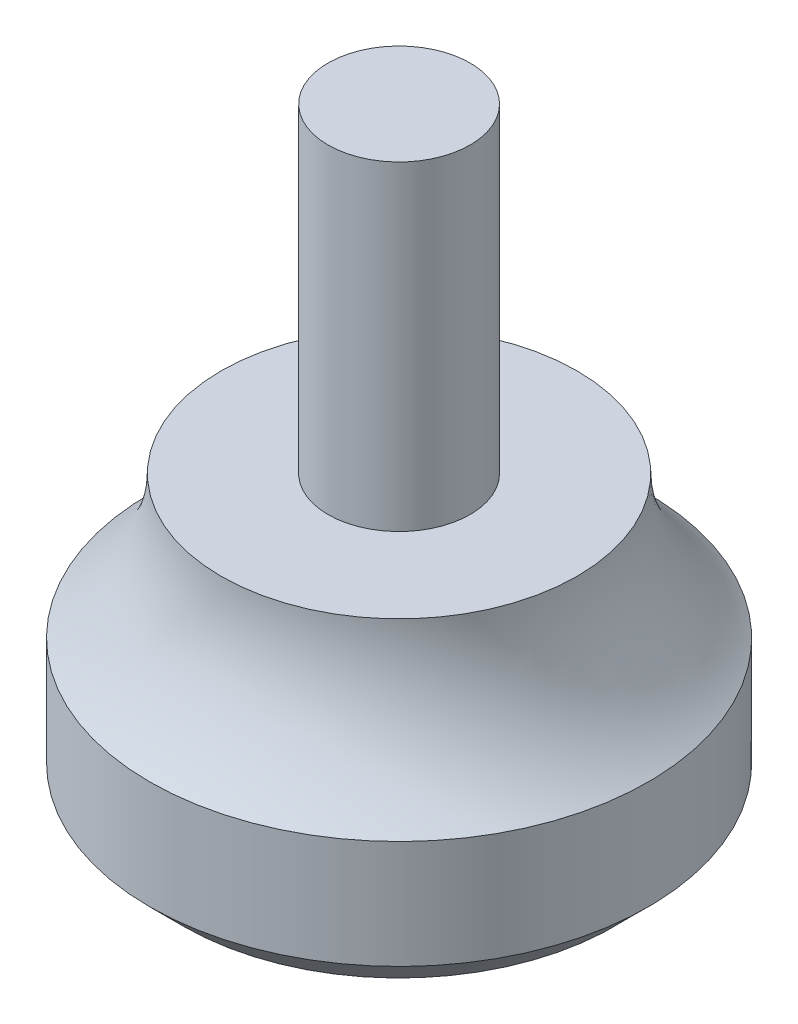
SolidWorks part; units mm, degrees
ref_plane "Front Plane" through (0, 0, 0) normal (0, 0, 1) x (1, 0, 0)
ref_plane "Top Plane" through (0, 0, 0) normal (0, 1, 0) x (1, 0, 0)
ref_plane "Right Plane" through (0, 0, 0) normal (1, 0, 0) x (0, 0, -1)
sketch "Sketch1" plane through (0, 0, 0) normal (0, 0, 1) x (1, 0, 0)
  line L0 (0, 0) -> (0, -11.1608) construction
  line L1 (0, 0) -> (0, 26.9748)
  line L5 (0, 0) -> (11.121, 0)
  line L6 (11.121, 0) -> (11.121, 6.35)
  line L8 (7.9375, 12.7) -> (3.1686, 12.7)
  line L9 (3.1686, 12.7) -> (3.1686, 26.9748)
  line L10 (3.1686, 26.9748) -> (0, 26.9748)
  arc A0 (11.121, 6.35) -> (7.9375, 12.7) centre (15.8623, 12.7) cw
  dimension "D4" = 7.9248
  dimension "D1" = 15.875
  dimension "D2" = 6.3373
  dimension "D3" = 26.9748
  dimension "D5" = 14.2748
  dimension "D6" = 20.6248
revolve "Revolve1" add sketch "Sketch1" angle 360 about L0
chamfer "Chamfer1" distance 1.524 angle 45 1 edges at (0, 0, 11.121)
